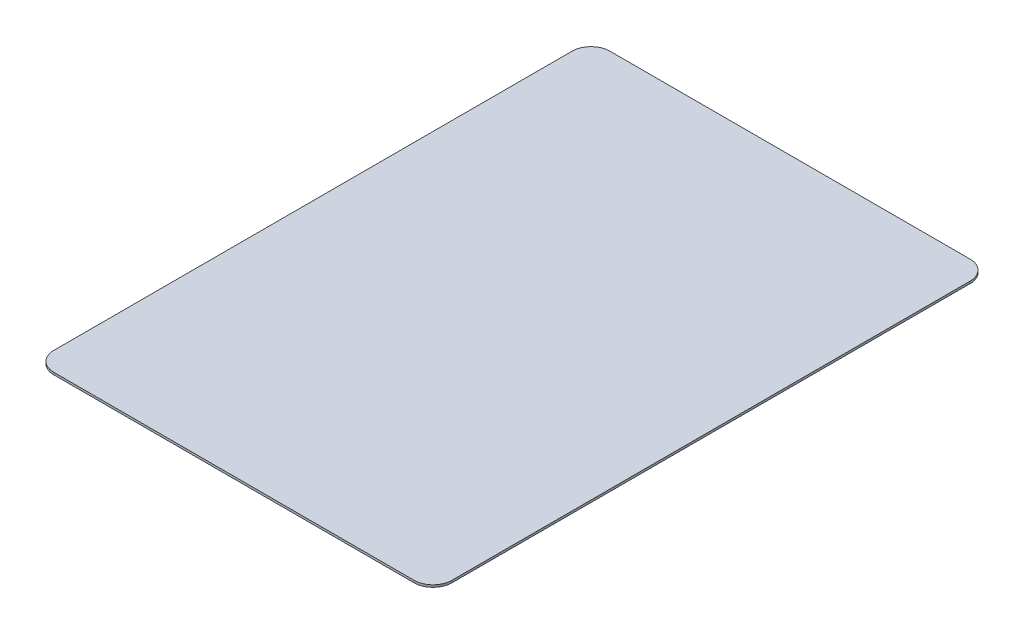
SolidWorks part; units mm, degrees
ref_plane "Front Plane" through (0, 0, 0) normal (0, 0, 1) x (1, 0, 0)
ref_plane "Top Plane" through (0, 0, 0) normal (0, 1, 0) x (1, 0, 0)
ref_plane "Right Plane" through (0, 0, 0) normal (1, 0, 0) x (0, 0, -1)
sketch "Sketch1" plane through (0, 0, 0) normal (0, 1, 0) x (1, 0, 0)
  line L1 (28.5, -44) -> (-28.5, -44)
  line L2 (31.5, -41) -> (31.5, 41)
  line L3 (28.5, 44) -> (-28.5, 44)
  line L4 (-31.5, -41) -> (-31.5, 41)
  line L5 (31.5, -44) -> (-31.5, 44) construction
  line L6 (31.5, 44) -> (-31.5, -44) construction
  arc A0 (-28.5, -44) -> (-31.5, -41) centre (-28.5, -41) cw
  arc A1 (28.5, -44) -> (31.5, -41) centre (28.5, -41) ccw
  arc A2 (31.5, 41) -> (28.5, 44) centre (28.5, 41) ccw
  arc A3 (-28.5, 44) -> (-31.5, 41) centre (-28.5, 41) ccw
  point P0 (0, 0)
  dimension "D3" = 3
  dimension "D1" = 88
  dimension "D2" = 63
extrude "Boss-Extrude1" add sketch "Sketch1" along normal blind 0.35
